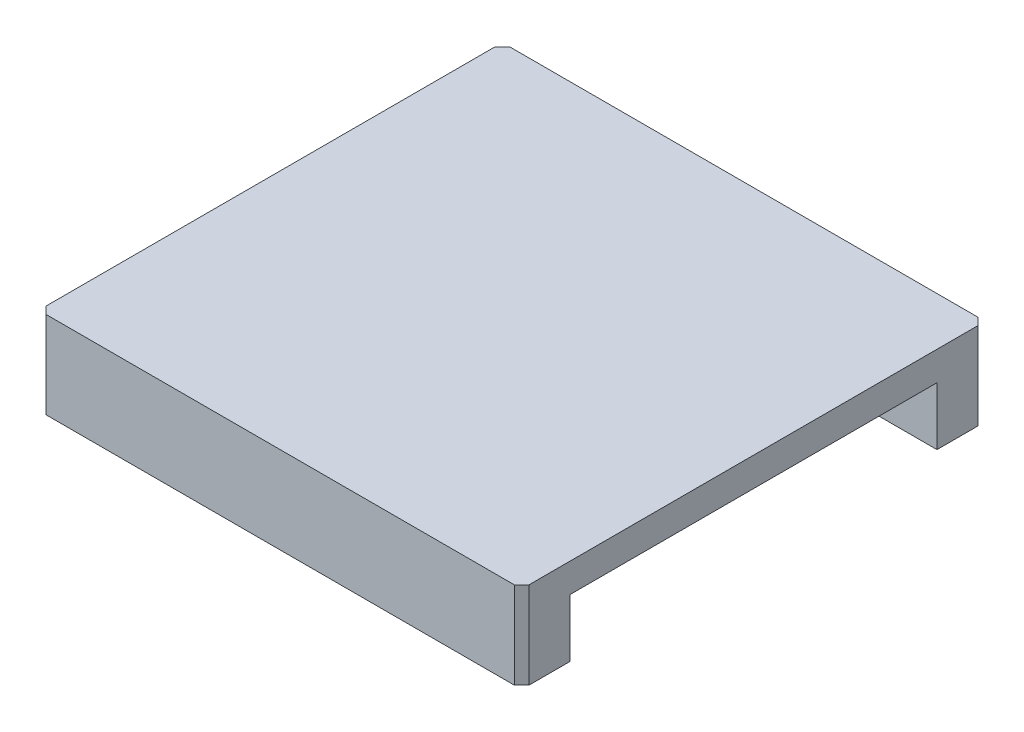
SolidWorks part; units mm, degrees
material "PLA"
ref_plane "Piano frontale" through (0, 0, 0) normal (0, 0, 1) x (1, 0, 0)
ref_plane "Piano superiore" through (0, 0, 0) normal (0, 1, 0) x (1, 0, 0)
ref_plane "Piano destro" through (0, 0, 0) normal (1, 0, 0) x (0, 0, -1)
sketch "Schizzo16" plane through (0, 0, 0) normal (1, 0, 0) x (0, 0, -1)
  line L0 (0, 0) -> (5, 0)
  line L1 (5, 0) -> (5, 6)
  line L2 (5, 6) -> (43, 6)
  line L3 (43, 6) -> (43, 0)
  line L4 (43, 0) -> (48, 0)
  line L5 (48, 0) -> (48, 9)
  line L6 (48, 9) -> (0, 9)
  line L7 (0, 9) -> (0, 0)
  dimension "D1" = 5
  dimension "D2" = 6
  dimension "D3" = 38
  dimension "D4" = 3
extrude "Estrusione-Estrusione9" add sketch "Schizzo16" along normal blind 50
chamfer "Smusso1" distance 0.75 angle 45 4 edges at (0, 4.5, 0) (0, 4.5, -48) (50, 4.5, -48) (50, 4.5, 0)
